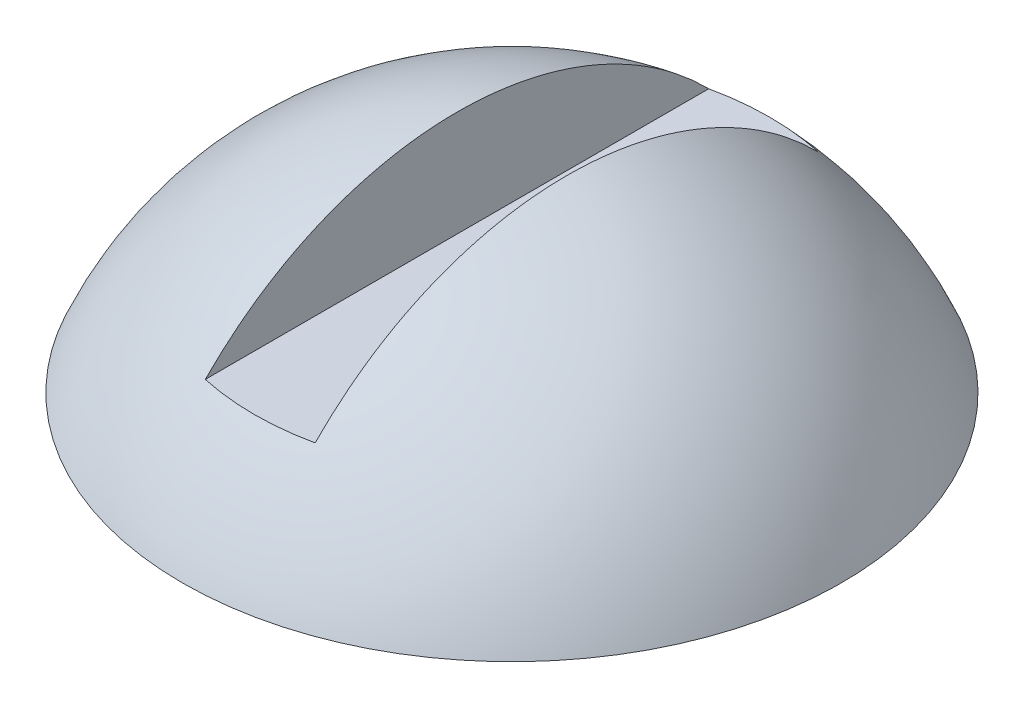
SolidWorks part; units mm, degrees
ref_plane "Alzado" through (0, 0, 0) normal (0, 0, 1) x (1, 0, 0)
ref_plane "Planta" through (0, 0, 0) normal (0, 1, 0) x (1, 0, 0)
ref_plane "Vista lateral" through (0, 0, 0) normal (1, 0, 0) x (0, 0, -1)
sketch "Croquis1" plane through (0, 0, 0) normal (1, 0, 0) x (0, 0, -1)
  line L0 (-3, 0) -> (0, 0)
  line L1 (0, 3.5457) -> (0, -2.9003) construction
  line L2 (0, 2) -> (0, 0)
  arc A0 (-3, 0) -> (0, 2) centre (0, -1.25) cw
  dimension "D2" = 2
  dimension "D1" = 3
revolve "Revolución1" add sketch "Croquis1" angle 360 about L1
ref_plane "Plano1" through (0, 2, 0) normal (0, 1, 0) x (1, 0, 0)
sketch "Croquis2" plane through (0, 2, 0) normal (0, 1, 0) x (1, 0, 0)
  line L1 (-0.5, 3) -> (0.5, 3)
  line L2 (-0.5, 3) -> (-0.5, -3)
  line L3 (-0.5, -3) -> (0.5, -3)
  line L4 (0.5, 3) -> (0.5, -3)
  circle A1 centre (0, 0) radius 3 construction
  point P6 (0, 3)
  dimension "D1" = 1
extrude "Cortar-Extruir1" cut sketch "Croquis2" against normal blind 1
